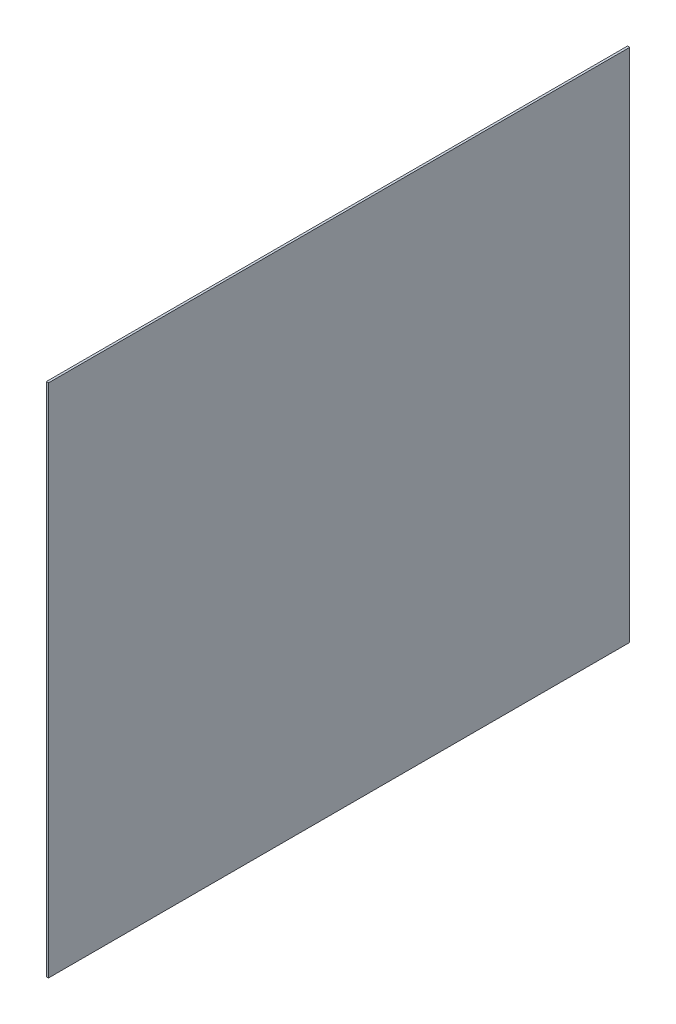
SolidWorks part; units mm, degrees
ref_plane "Front Plane" through (0, 0, 0) normal (0, 0, 1) x (1, 0, 0)
ref_plane "Top Plane" through (0, 0, 0) normal (0, 1, 0) x (1, 0, 0)
ref_plane "Right Plane" through (0, 0, 0) normal (1, 0, 0) x (0, 0, -1)
sketch "Sketch2" plane through (0, 0, 0) normal (1, 0, 0) x (0, 0, -1)
  line L1 (0, 0) -> (412.496, 0)
  line L2 (0, 0) -> (0, 365.76)
  line L3 (0, 365.76) -> (412.496, 365.76)
  line L4 (412.496, 0) -> (412.496, 365.76)
extrude "PCB" add sketch "Sketch2" along normal blind 1.5875
